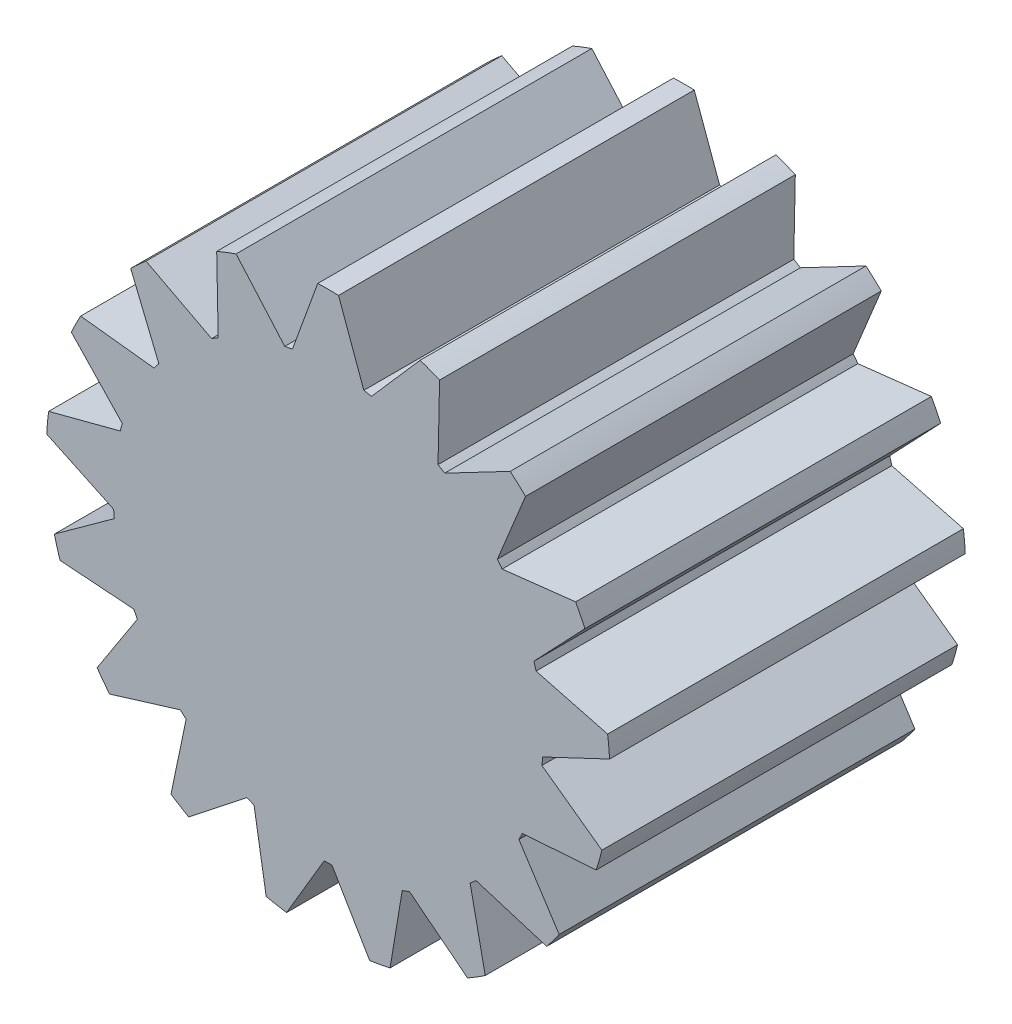
SolidWorks part; units mm, degrees
ref_plane "Front Plane" through (0, 0, 0) normal (0, 0, 1) x (1, 0, 0)
ref_plane "Top Plane" through (0, 0, 0) normal (0, 1, 0) x (1, 0, 0)
ref_plane "Right Plane" through (0, 0, 0) normal (1, 0, 0) x (0, 0, -1)
sketch "Sketch2" plane through (0, 0, 0) normal (0, 0, 1) x (1, 0, 0)
  line L0 (-4.366, 25.9419) -> (-1.27, 34.4482)
  line L1 (1.27, 34.4482) -> (4.366, 25.9419)
  line L2 (0, 0) -> (0, 34.4716) construction
  line L3 (5.3001, 25.7673) -> (11.2599, 32.5808)
  line L4 (13.6284, 31.6632) -> (13.4425, 22.613)
  line L5 (14.2504, 22.1127) -> (22.2691, 26.3131)
  line L6 (24.1461, 24.6019) -> (20.7035, 16.23)
  line L7 (21.2762, 15.4716) -> (30.2707, 16.4917)
  line L8 (31.4029, 14.218) -> (25.1684, 7.655)
  line L9 (25.4284, 6.741) -> (34.1841, 4.4431)
  line L10 (34.4184, 1.9139) -> (26.2341, -1.9538)
  line L11 (26.1464, -2.9) -> (33.4807, -8.2057)
  line L12 (32.7856, -10.6487) -> (23.7568, -11.2987)
  line L13 (23.3332, -12.1493) -> (28.2556, -19.7462)
  line L14 (26.7249, -21.7732) -> (18.071, -19.1177)
  line L15 (17.3687, -19.7579) -> (19.2144, -28.6199)
  line L16 (17.0549, -29.957) -> (9.9446, -24.3547)
  line L17 (9.0585, -24.698) -> (7.5782, -33.6283)
  line L18 (5.0815, -34.095) -> (0.4751, -26.3025)
  line L19 (-0.4751, -26.3025) -> (-5.0815, -34.095)
  line L20 (-7.5782, -33.6283) -> (-9.0585, -24.698)
  line L21 (-9.9446, -24.3547) -> (-17.0549, -29.957)
  line L22 (-19.2144, -28.6199) -> (-17.3687, -19.7579)
  line L23 (-18.071, -19.1177) -> (-26.7249, -21.7732)
  line L24 (-28.2556, -19.7462) -> (-23.3332, -12.1493)
  line L25 (-23.7568, -11.2987) -> (-32.7856, -10.6487)
  line L26 (-33.4807, -8.2057) -> (-26.1464, -2.9)
  line L27 (-26.2341, -1.9538) -> (-34.4184, 1.9139)
  line L28 (-34.1841, 4.4431) -> (-25.4284, 6.741)
  line L29 (-25.1684, 7.655) -> (-31.4029, 14.218)
  line L30 (-30.2707, 16.4917) -> (-21.2762, 15.4716)
  line L31 (-20.7035, 16.23) -> (-24.1461, 24.6019)
  line L32 (-22.2691, 26.3131) -> (-14.2504, 22.1127)
  line L33 (-13.4425, 22.613) -> (-13.6284, 31.6632)
  line L34 (-11.2599, 32.5808) -> (-5.3001, 25.7673)
  arc A0 (-4.366, 25.9419) -> (-5.3001, 25.7673) centre (0, 0) ccw
  arc A1 (1.27, 34.4482) -> (-1.27, 34.4482) centre (0, 0) ccw
  arc A2 (13.6284, 31.6632) -> (11.2599, 32.5808) centre (0, 0) ccw
  arc A3 (24.1461, 24.6019) -> (22.2691, 26.3131) centre (0, 0) ccw
  arc A4 (31.4029, 14.218) -> (30.2707, 16.4917) centre (0, 0) ccw
  arc A5 (34.4184, 1.9139) -> (34.1841, 4.4431) centre (0, 0) ccw
  arc A6 (32.7856, -10.6487) -> (33.4807, -8.2057) centre (0, 0) ccw
  arc A7 (26.7249, -21.7732) -> (28.2556, -19.7462) centre (0, 0) ccw
  arc A8 (17.0549, -29.957) -> (19.2144, -28.6199) centre (0, 0) ccw
  arc A9 (5.0815, -34.095) -> (7.5782, -33.6283) centre (0, 0) ccw
  arc A10 (-7.5782, -33.6283) -> (-5.0815, -34.095) centre (0, 0) ccw
  arc A11 (-19.2144, -28.6199) -> (-17.0549, -29.957) centre (0, 0) ccw
  arc A12 (-28.2556, -19.7462) -> (-26.7249, -21.7732) centre (0, 0) ccw
  arc A13 (-33.4807, -8.2057) -> (-32.7856, -10.6487) centre (0, 0) ccw
  arc A14 (-34.1841, 4.4431) -> (-34.4184, 1.9139) centre (0, 0) ccw
  arc A15 (-30.2707, 16.4917) -> (-31.4029, 14.218) centre (0, 0) ccw
  arc A16 (-22.2691, 26.3131) -> (-24.1461, 24.6019) centre (0, 0) ccw
  arc A17 (-11.2599, 32.5808) -> (-13.6284, 31.6632) centre (0, 0) ccw
  arc A18 (-13.4425, 22.613) -> (-14.2504, 22.1127) centre (0, 0) ccw
  arc A19 (-20.7035, 16.23) -> (-21.2762, 15.4716) centre (0, 0) ccw
  arc A20 (-25.1684, 7.655) -> (-25.4284, 6.741) centre (0, 0) ccw
  arc A21 (-26.2341, -1.9538) -> (-26.1464, -2.9) centre (0, 0) ccw
  arc A22 (-23.7568, -11.2987) -> (-23.3332, -12.1493) centre (0, 0) ccw
  arc A23 (-18.071, -19.1177) -> (-17.3687, -19.7579) centre (0, 0) ccw
  arc A24 (-9.9446, -24.3547) -> (-9.0585, -24.698) centre (0, 0) ccw
  arc A25 (-0.4751, -26.3025) -> (0.4751, -26.3025) centre (0, 0) ccw
  arc A26 (9.0585, -24.698) -> (9.9446, -24.3547) centre (0, 0) ccw
  arc A27 (17.3687, -19.7579) -> (18.071, -19.1177) centre (0, 0) ccw
  arc A28 (23.3332, -12.1493) -> (23.7568, -11.2987) centre (0, 0) ccw
  arc A29 (26.1464, -2.9) -> (26.2341, -1.9538) centre (0, 0) ccw
  arc A30 (25.4284, 6.741) -> (25.1684, 7.655) centre (0, 0) ccw
  arc A31 (21.2762, 15.4716) -> (20.7035, 16.23) centre (0, 0) ccw
  arc A32 (14.2504, 22.1127) -> (13.4425, 22.613) centre (0, 0) ccw
  arc A33 (5.3001, 25.7673) -> (4.366, 25.9419) centre (0, 0) ccw
  point P75 (0, 0)
  dimension "D1" = 52.6136
  dimension "D2" = 68.9432
  dimension "D3" = 1.27
  dimension "D4" = 1.27
  dimension "D5" = 20
  dimension "D6" = 20
  dimension "D7" = 17
extrude "Boss-Extrude1" add sketch "Sketch2" along normal blind 43.5102
